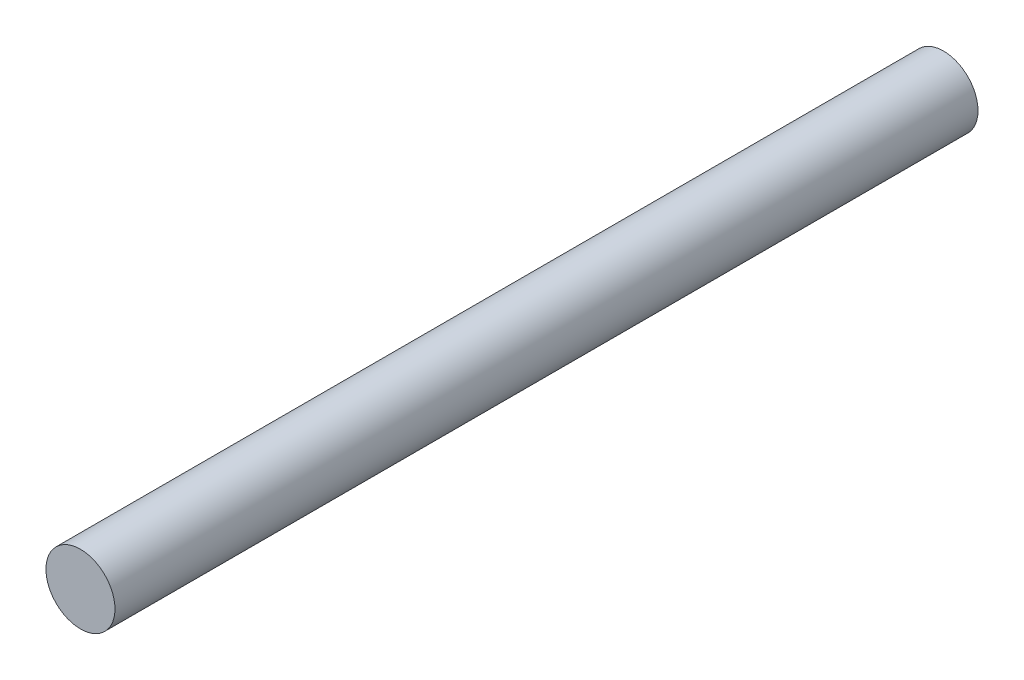
SolidWorks part; units mm, degrees
ref_plane "Front Plane" through (0, 0, 0) normal (0, 0, 1) x (1, 0, 0)
ref_plane "Top Plane" through (0, 0, 0) normal (0, 1, 0) x (1, 0, 0)
ref_plane "Right Plane" through (0, 0, 0) normal (1, 0, 0) x (0, 0, -1)
sketch "Sketch1" plane through (0, 0, 0) normal (0, 0, 1) x (1, 0, 0)
  circle A0 centre (0, 0) radius 4
  dimension "D1" = 8
extrude "Boss-Extrude1" add sketch "Sketch1" along normal blind 100
